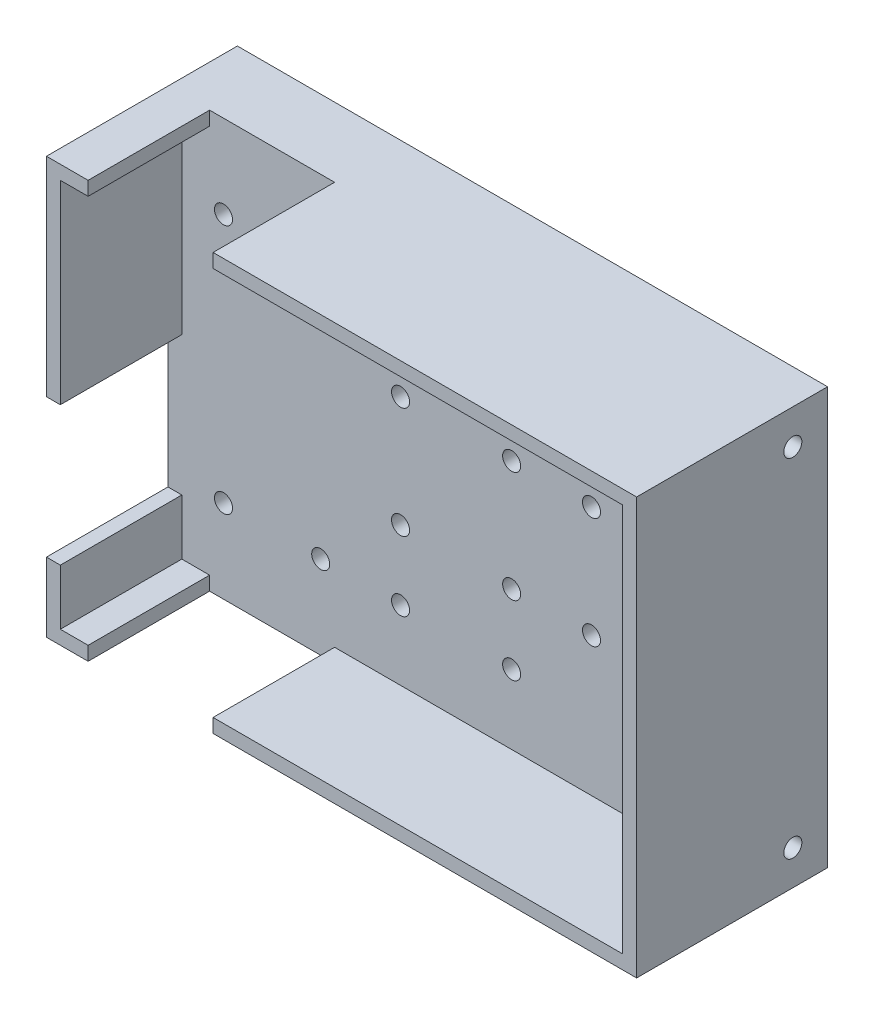
SolidWorks part; units mm, degrees
ref_plane "Front Plane" through (0, 0, 0) normal (1, 0, 0) x (0, 1, 0)
ref_plane "Top Plane" through (0, 0, 0) normal (0, 0, 1) x (0, 1, 0)
ref_plane "Right Plane" through (0, 0, 0) normal (0, 1, 0) x (-1, 0, 0)
sketch "Sketch1" plane through (0, 0, 0) normal (0, 0, 1) x (0, 1, 0)
  line L1 (-38.1, -53.975) -> (38.1, -53.975)
  line L2 (-38.1, -53.975) -> (-38.1, 53.975)
  line L3 (-38.1, 53.975) -> (38.1, 53.975)
  line L4 (38.1, -53.975) -> (38.1, 53.975)
  line L5 (-38.1, -53.975) -> (38.1, 53.975) construction
  line L6 (-38.1, 53.975) -> (38.1, -53.975) construction
  point P0 (0, 0)
  dimension "D1" = 76.2
  dimension "D2" = 107.95
extrude "BASE" add sketch "Sketch1" along normal blind 12.7
sketch "Sketch2" plane through (0, 0, 12.7) normal (0, 0, 1) x (1, 0, 0)
  line L0 (-43.815, 22.86) -> (-43.815, -22.86) construction
  line L1 (-46.355, 25.4) -> (-23.495, 25.4) construction
  line L2 (-46.355, 25.4) -> (-46.355, -25.4) construction
  line L3 (-46.355, -25.4) -> (-23.495, -25.4) construction
  line L4 (-23.495, 25.4) -> (-23.495, -25.4) construction
  line L5 (-43.815, -22.86) -> (-26.035, -22.86) construction
  line L6 (-26.035, 22.86) -> (-26.035, -22.86) construction
  line L7 (-43.815, 22.86) -> (-26.035, 22.86) construction
  line L8 (-11.43, 22.86) -> (-11.43, 10.16) construction
  line L9 (-13.97, 25.4) -> (11.43, 25.4) construction
  line L10 (-13.97, 25.4) -> (-13.97, 7.62) construction
  line L11 (-13.97, 7.62) -> (11.43, 7.62) construction
  line L12 (11.43, 25.4) -> (11.43, 7.62) construction
  line L13 (-11.43, 10.16) -> (8.89, 10.16) construction
  line L14 (8.89, 22.86) -> (8.89, 10.16) construction
  line L15 (-11.43, 22.86) -> (8.89, 22.86) construction
  line L16 (-11.43, -10.16) -> (-11.43, -22.86) construction
  line L17 (-13.97, -7.62) -> (11.43, -7.62) construction
  line L18 (-13.97, -7.62) -> (-13.97, -25.4) construction
  line L19 (-13.97, -25.4) -> (11.43, -25.4) construction
  line L20 (11.43, -7.62) -> (11.43, -25.4) construction
  line L21 (-11.43, -22.86) -> (8.89, -22.86) construction
  line L22 (8.89, -10.16) -> (8.89, -22.86) construction
  line L23 (-11.43, -10.16) -> (8.89, -10.16) construction
  line L24 (23.495, 10.16) -> (23.495, -10.16) construction
  line L25 (20.955, 12.7) -> (46.355, 12.7) construction
  line L26 (20.955, 12.7) -> (20.955, -12.7) construction
  line L27 (20.955, -12.7) -> (46.355, -12.7) construction
  line L28 (46.355, 12.7) -> (46.355, -12.7) construction
  line L29 (23.495, -10.16) -> (43.815, -10.16) construction
  line L30 (43.815, 10.16) -> (43.815, -10.16) construction
  line L31 (23.495, 10.16) -> (43.815, 10.16) construction
  line L32 (-28.0202, 0) -> (49971.9798, 0) construction
  line L33 (-53.975, 38.1) -> (-53.975, -38.1) construction
  line L38 (-46.355, 25.4) -> (46.355, 25.4) construction
  line L39 (-46.355, 25.4) -> (-46.355, -25.4) construction
  line L40 (-46.355, -25.4) -> (46.355, -25.4) construction
  line L41 (46.355, 25.4) -> (46.355, -25.4) construction
  line L42 (0, 0) -> (0, 50000) construction
  line L44 (53.975, 38.1) -> (-53.975, 38.1) construction
  circle A0 centre (-43.815, 22.86) radius 1.65
  circle A1 centre (-26.035, 22.86) radius 1.65
  circle A2 centre (-43.815, -22.86) radius 1.65
  circle A3 centre (-26.035, -22.86) radius 1.65
  circle A4 centre (-11.43, -22.86) radius 1.65
  circle A5 centre (-11.43, -10.16) radius 1.65
  circle A6 centre (8.89, -10.16) radius 1.65
  circle A7 centre (8.89, -22.86) radius 1.65
  circle A8 centre (23.495, -10.16) radius 1.65
  circle A9 centre (43.815, -10.16) radius 1.65
  circle A10 centre (43.815, 10.16) radius 1.65
  circle A11 centre (23.495, 10.16) radius 1.65
  circle A13 centre (-11.43, 10.16) radius 1.65
  circle A14 centre (8.89, 22.86) radius 1.65
  circle A15 centre (-11.43, 22.86) radius 1.65
  circle A16 centre (8.89, 10.16) radius 1.65
  point P34 (-23.495, 0)
  point P35 (20.955, 0)
  point P38 (-53.975, 0)
  point P301 (0, 25.4)
  point P304 (0, 38.1)
  dimension "D1" = 2.54
  dimension "D15" = 3.3
  dimension "D16" = 3.3
  dimension "D17" = 3.3
  dimension "D18" = 3.3
  dimension "D19" = 3.3
  dimension "D20" = 3.3
  dimension "D21" = 3.3
  dimension "D22" = 3.3
  dimension "D23" = 3.3
  dimension "D24" = 3.3
  dimension "D25" = 3.3
  dimension "D26" = 3.3
  dimension "D27" = 3.3
  dimension "D28" = 3.3
  dimension "D29" = 3.3
  dimension "D30" = 3.3
  dimension "D5" = 22.86
  dimension "D6" = 50.8
  dimension "D7" = 25.4
  dimension "D8" = 17.78
  dimension "D9" = 25.4
  dimension "D10" = 17.78
  dimension "D11" = 25.4
  dimension "D12" = 25.4
  dimension "D13" = 9.525
  dimension "D14" = 9.525
  dimension "D2" = 2.54
  dimension "D3" = 2.54
  dimension "D4" = 2.54
sketch "Sketch3" plane through (0, 0, 12.7) normal (0, 0, 1) x (1, 0, 0)
  line L0 (-51.435, 35.56) -> (-51.435, -35.56)
  line L1 (-53.975, 38.1) -> (53.975, 38.1)
  line L2 (-53.975, 38.1) -> (-53.975, -38.1)
  line L3 (-53.975, -38.1) -> (53.975, -38.1)
  line L4 (53.975, 38.1) -> (53.975, -38.1)
  line L5 (-51.435, -35.56) -> (51.435, -35.56)
  line L6 (51.435, 35.56) -> (51.435, -35.56)
  line L7 (-51.435, 35.56) -> (51.435, 35.56)
  dimension "D1" = 2.54
extrude "WALLS" add sketch "Sketch3" along normal blind 22.225
sketch "Sketch4" plane through (0, 0, 34.925) normal (0, 0, 1) x (1, 0, 0)
  line L0 (53.975, 38.1) -> (-53.975, 38.1) construction
  line L5 (-46.355, 38.1) -> (-23.495, 38.1)
  line L6 (-46.355, 38.1) -> (-46.355, 0)
  line L7 (-46.355, -38.1) -> (-23.495, -38.1)
  line L8 (-23.495, 38.1) -> (-23.495, -38.1)
  line L9 (-53.975, -38.1) -> (53.975, -38.1) construction
  line L11 (-23.495, 25.4) -> (-23.495, -25.4) construction
  line L12 (-46.355, 25.4) -> (-46.355, -25.4) construction
  line L13 (-53.975, 38.1) -> (-53.975, -38.1) construction
  line L14 (-46.355, 0) -> (-53.975, 0)
  line L16 (-46.355, -25.4) -> (-53.975, -25.4)
  line L17 (-53.975, 0) -> (-53.975, -25.4)
  line L18 (-46.355, -25.4) -> (-23.495, -25.4) construction
  line L19 (-46.355, -25.4) -> (-46.355, -38.1)
  line L20 (-200028.0202, 0) -> (249971.9798, 0) construction
extrude "Cut-Extrude1" cut sketch "Sketch4" against normal blind 22.225
extrude "Cut-Extrude2" cut sketch "Sketch2" against normal blind 7
sketch "Sketch6" plane through (-53.975, 0, 0) normal (-1, 0, 0) x (0, -1, 0)
  line L0 (0, 12.7) -> (0, 0) construction
  line L1 (0, 6.35) -> (50000, 6.35) construction
  line L2 (-38.1, 34.925) -> (-38.1, 0) construction
  line L3 (38.1, 34.925) -> (38.1, 0) construction
  circle A0 centre (-31.75, 6.35) radius 1.65
  circle A1 centre (31.75, 6.35) radius 1.65
  point P6 (0, 6.35)
  dimension "D1" = 3.3
  dimension "D2" = 3.3
sketch "Sketch7" plane through (53.975, 0, 0) normal (1, 0, 0) x (0, 1, 0)
  line L0 (38.1, 34.925) -> (38.1, 0) construction
  line L1 (-38.1, 0) -> (38.1, 0) construction
  line L2 (-38.1, 0) -> (-38.1, 12.7) construction
  line L3 (-38.1, 12.7) -> (38.1, 12.7) construction
  line L4 (38.1, 0) -> (38.1, 12.7) construction
  line L5 (0, 12.7) -> (0, 0) construction
  line L6 (0, 6.35) -> (50000, 6.35) construction
  circle A0 centre (-31.75, 6.35) radius 1.65
  circle A1 centre (31.75, 6.35) radius 1.65
  point P13 (0, 6.35)
  dimension "D1" = 12.7
  dimension "D2" = 3.3
  dimension "D3" = 3.3
  dimension "D5" = 6.35
extrude "Cut-Extrude3" cut sketch "Sketch6" against normal blind 7
extrude "Cut-Extrude4" cut sketch "Sketch7" against normal blind 7
equation "\"LENGTH\"= 3in"
equation "\"WIDTH\"= 4.25in"
equation "\"WALL_HEIGHT\"= 1 * 7 / 8"
equation "\"WALL_WIDTH\"= 0.1in"
equation "\"D2@Sketch1\"=\"WIDTH\""
equation "\"D1@Sketch1\"=\"LENGTH\""
equation "\"BASE_HEIGHT\"= 0.5in"
equation "\"D1@BASE\" = \"BASE_HEIGHT\""
equation "\"D1@Sketch3\"=\"WALL_WIDTH\""
equation "\"D1@WALLS\" = \"WALL_HEIGHT\""
equation "\"D1@Cut-Extrude1\"=\"WALL_HEIGHT\""
equation "\"M2.5_INSERT_HOLE\"= 3.3mm"
equation "\"M2.5_INSERT_DEPTH\"= 7mm"
equation "\"D15@Sketch2\"=\"M2.5_INSERT_HOLE\""
equation "\"D16@Sketch2\"=\"M2.5_INSERT_HOLE\""
equation "\"D17@Sketch2\"=\"M2.5_INSERT_HOLE\""
equation "\"D18@Sketch2\"=\"M2.5_INSERT_HOLE\""
equation "\"D19@Sketch2\"=\"M2.5_INSERT_HOLE\""
equation "\"D20@Sketch2\"=\"M2.5_INSERT_HOLE\""
equation "\"D21@Sketch2\"=\"M2.5_INSERT_HOLE\""
equation "\"D22@Sketch2\"=\"M2.5_INSERT_HOLE\""
equation "\"D23@Sketch2\"=\"M2.5_INSERT_HOLE\""
equation "\"D24@Sketch2\"=\"M2.5_INSERT_HOLE\""
equation "\"D25@Sketch2\"=\"M2.5_INSERT_HOLE\""
equation "\"D26@Sketch2\"=\"M2.5_INSERT_HOLE\""
equation "\"D27@Sketch2\"=\"M2.5_INSERT_HOLE\""
equation "\"D28@Sketch2\"=\"M2.5_INSERT_HOLE\""
equation "\"D29@Sketch2\"=\"M2.5_INSERT_HOLE\""
equation "\"D30@Sketch2\"=\"M2.5_INSERT_HOLE\""
equation "\"D1@Cut-Extrude2\"=\"M2.5_INSERT_DEPTH\""
equation "\"D1@Sketch6\"=\"M2.5_INSERT_HOLE\""
equation "\"D2@Sketch6\"=\"M2.5_INSERT_HOLE\""
equation "\"COVER_SCREW_CLEARANCE\"= 0.25in"
equation "\"D3@Sketch6\"=\"COVER_SCREW_CLEARANCE\""
equation "\"D4@Sketch6\"=\"COVER_SCREW_CLEARANCE\""
equation "\"D1@Sketch7\"=\"BASE_HEIGHT\""
equation "\"D2@Sketch7\"=\"M2.5_INSERT_HOLE\""
equation "\"D3@Sketch7\"=\"M2.5_INSERT_HOLE\""
equation "\"D5@Sketch7\"=\"COVER_SCREW_CLEARANCE\""
equation "\"D1@Cut-Extrude3\"=\"M2.5_INSERT_DEPTH\""
equation "\"D1@Cut-Extrude4\"=\"M2.5_INSERT_DEPTH\""
